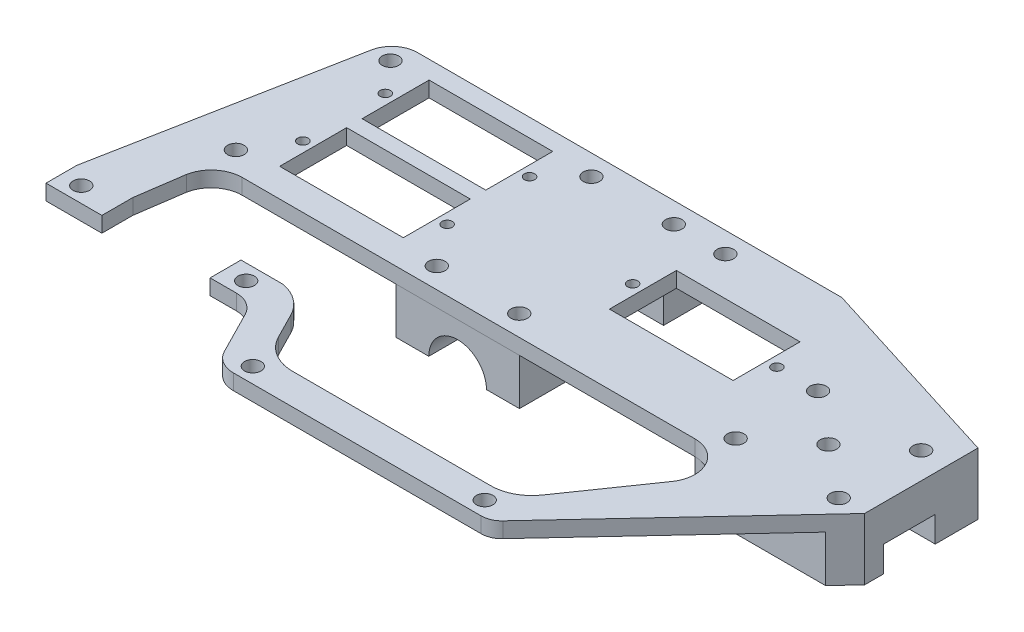
SolidWorks part; units mm, degrees
ref_plane "Спереди" through (0, 0, 0) normal (0, 0, 1) x (1, 0, 0)
ref_plane "Сверху" through (0, 0, 0) normal (0, 1, 0) x (1, 0, 0)
ref_plane "Справа" through (0, 0, 0) normal (1, 0, 0) x (0, 0, -1)
sketch "Эскиз1" plane through (0, 0, 0) normal (0, 1, 0) x (1, 0, 0)
  line L0 (0, 20) -> (0, -20) construction
  line L1 (16, 6.5) -> (40, 6.5)
  line L2 (-40, 14.5) -> (-16, 14.5)
  line L3 (-40, 14.5) -> (-40, 1.5)
  line L4 (-40, 1.5) -> (-16, 1.5)
  line L5 (-16, 14.5) -> (-16, 1.5)
  line L6 (-40, 14.5) -> (-16, 1.5) construction
  line L7 (-40, 1.5) -> (-16, 14.5) construction
  line L8 (-40, -1.5) -> (-16, -1.5)
  line L9 (-40, -1.5) -> (-40, -14.5)
  line L10 (-40, -14.5) -> (-16, -14.5)
  line L11 (-16, -1.5) -> (-16, -14.5)
  line L12 (-40, -1.5) -> (-16, -14.5) construction
  line L13 (-40, -14.5) -> (-16, -1.5) construction
  line L14 (-28, 8) -> (-28, -8) construction
  line L15 (0, 20) -> (-56.8521, 20) construction
  line L16 (0, 20) -> (59.9648, 20) construction
  line L17 (0, -20) -> (57.5525, -20) construction
  line L18 (0, -20) -> (-56.8521, -20) construction
  line L19 (16, 6.5) -> (16, -6.5)
  line L20 (16, -6.5) -> (40, -6.5)
  line L21 (40, 6.5) -> (40, -6.5)
  line L22 (16, 6.5) -> (40, -6.5) construction
  line L23 (16, -6.5) -> (40, 6.5) construction
  line L24 (28, 20) -> (28, -20) construction
  line L25 (-56.8521, 14) -> (93.1479, 14) construction
  line L26 (-56.8521, -16) -> (93.1479, -16) construction
  line L27 (-40, -37) -> (-56, -37) construction
  line L28 (-40, -37) -> (-24, -37) construction
  line L29 (-40, -14.5) -> (-40, -37) construction
  line L30 (-59.8465, -34) -> (-19.8465, -34) construction
  line L31 (-19.8465, -34) -> (-19.8465, -40) construction
  line L32 (-19.8465, -40) -> (-59.8465, -40) construction
  line L33 (-59.8465, -40) -> (-59.8465, -34) construction
  line L34 (-59.8465, -34) -> (-49.8878, 18)
  line L35 (36.6127, 18) -> (-49.8878, 18)
  line L36 (36.6127, 18) -> (75.1122, 5.9202)
  line L37 (-47.6771, -24.9007) -> (-49.0001, -34)
  line L38 (50, -16) -> (70, -16) construction
  line L39 (-59.8465, -34) -> (-59.8465, -40)
  line L40 (-59.8465, -40) -> (-19.8465, -40)
  line L41 (-19.8465, -40) -> (-14.2549, -50.9742)
  line L42 (-9.7998, -53.7042) -> (38.319, -53.7042)
  line L43 (75.1122, 5.9202) -> (75.1122, -16.0798)
  line L44 (50, 0) -> (50, -16) construction
  line L45 (-4.2859, -47.7018) -> (34.1658, -47.7018)
  line L46 (-49.0001, -34) -> (-22.2977, -34)
  line L47 (-13.9887, -38.2804) -> (-11.4139, -43.3337)
  line L48 (-41.7786, -20) -> (46.0945, -20)
  line L49 (40.7412, -44.2586) -> (51.0261, -29.4176)
  line L50 (-20.5914, -50.7042) -> (71.7063, -50.7042) construction
  line L51 (-20.5914, -53.7042) -> (73.7938, -53.7042) construction
  line L52 (0, -16) -> (0, -104.4432) construction
  line L53 (-47, 14) -> (-47, -16) construction
  line L54 (50, 0) -> (70, -16) construction
  line L55 (-44.6457, 8) -> (-11.6511, 8) construction
  line L56 (-47.6771, -8) -> (-3.6396, -8) construction
  line L57 (8, 0) -> (46.0945, 0) construction
  line L58 (50, 0) -> (70, 0) construction
  line L59 (75.1122, -16.0798) -> (41.2457, -52.4308)
  line L60 (-49.0001, -34) -> (-49.0001, -40) construction
  line L61 (-22.2977, -34) -> (-19.8465, -34)
  circle A0 centre (-8, 14) radius 1.6
  circle A1 centre (8, 14) radius 1.6
  circle A2 centre (-8, -16) radius 1.6
  circle A3 centre (8, -16) radius 1.6
  circle A4 centre (-47, 14) radius 1.6
  circle A5 centre (70, 0) radius 1.6
  circle A6 centre (50, 0) radius 1.6
  circle A7 centre (18, 14) radius 1.6
  circle A8 centre (-47, -16) radius 1.6
  circle A9 centre (-56, -37) radius 1.6
  circle A10 centre (-24, -37) radius 1.6
  circle A11 centre (50, -16) radius 1.6
  circle A12 centre (70, -16) radius 1.6
  arc A13 (-41.7786, -20) -> (-47.6771, -24.9007) centre (-41.7786, -26) ccw
  arc A14 (-19.8465, -34) -> (-13.9887, -38.2804) centre (-21.3286, -42.1767) cw
  arc A15 (-4.2859, -47.7018) -> (-11.4139, -43.3337) centre (-4.2859, -39.7018) cw
  arc A16 (40.7412, -44.2586) -> (34.1658, -47.7018) centre (34.1658, -39.7018) cw
  arc A17 (51.0261, -29.4176) -> (46.0945, -20) centre (46.0945, -26) ccw
  arc A18 (41.2457, -52.4308) -> (38.319, -53.7042) centre (38.319, -49.7042) cw
  arc A19 (-9.7998, -53.7042) -> (-14.2549, -50.9742) centre (-9.7998, -48.7042) cw
  circle A20 centre (-9, -50.7042) radius 1.6
  circle A21 centre (36, -50.7042) radius 1.6
  circle A22 centre (60, -8) radius 1.6
  circle A23 centre (-42, -8) radius 1
  circle A24 centre (-14, -8) radius 1
  circle A25 centre (-42, 8) radius 1
  circle A26 centre (-14, 8) radius 1
  circle A27 centre (14, 0) radius 1
  circle A28 centre (42, 0) radius 1
  point P2 (-28, 8)
  point P7 (0, 0)
  point P10 (28, 0)
  point P11 (-28, -8)
  point P35 (0, 14)
  point P41 (0, -16)
  point P77 (-46.7637, -20)
  point P86 (40.0593, -53.7042)
  point P92 (-49.0001, -34)
  dimension "D10" = 16
  dimension "D12" = 16
  dimension "D14" = 10
  dimension "D18" = 40
  dimension "D23" = 20
  dimension "D26" = 6
  dimension "D31" = 125
  dimension "D32" = 3
  dimension "D33" = 45
  dimension "D36" = 28
  dimension "D21" = 4
  dimension "D1" = 13
  dimension "D2" = 24
  dimension "D3" = 28
  dimension "D4" = 28
  dimension "D5" = 20
  dimension "D6" = 12
  dimension "D7" = 3
  dimension "D8" = 6
  dimension "D9" = 4
  dimension "D11" = 8
  dimension "D13" = 8
  dimension "D15" = 20
  dimension "D16" = 50
  dimension "D17" = 32
  dimension "D19" = 6
  dimension "D20" = 3
  dimension "D22" = 6.0024
  dimension "D24" = 14
  dimension "D25" = 36
  dimension "D27" = 6
  dimension "D29" = 14
  dimension "D30" = 22
  dimension "D34" = 40
  dimension "D35" = 47
  dimension "D37" = 28
  dimension "D38" = 28
  dimension "D39" = 14
  dimension "D40" = 14
  dimension "D41" = 14
  dimension "D42" = 16
  dimension "D43" = 2
extrude "Бобышка-Вытянуть1" add sketch "Эскиз1" along normal blind 3
sketch "Эскиз2" plane through (0, 0, 0) normal (0, 1, 0) x (1, 0, 0)
  line L0 (46.1017, 15.0227) -> (46.0945, -20)
  line L2 (75.1122, 5.9202) -> (36.6127, 18) construction
  line L4 (46.0945, -20) -> (71.46, -20)
  line L10 (0, 18) -> (0, -19.9611) construction
  line L11 (12, 8) -> (-12, 8)
  line L12 (12, 8) -> (12, 18)
  line L13 (12, 18) -> (-12, 18)
  line L14 (-12, 8) -> (-12, 18)
  line L15 (12, 8) -> (-12, 18) construction
  line L16 (12, 18) -> (-12, 8) construction
  line L17 (12, -19.9611) -> (-12, -19.9611)
  line L18 (12, -19.9611) -> (12, -9.9611)
  line L19 (12, -9.9611) -> (-12, -9.9611)
  line L20 (-12, -19.9611) -> (-12, -9.9611)
  line L21 (12, -19.9611) -> (-12, -9.9611) construction
  line L22 (12, -9.9611) -> (-12, -19.9611) construction
  line L24 (75.1122, -16.0798) -> (75.1122, 5.9202)
  line L25 (41.2457, -52.4308) -> (75.1122, -16.0798) construction
  line L26 (71.46, -20) -> (75.1122, -16.0798)
  line L27 (46.1017, 15.0227) -> (75.1122, 5.9202)
  line L28 (36.6127, 18) -> (-49.8878, 18) construction
  circle A0 centre (50, 0) radius 1.6
  circle A1 centre (70, 0) radius 1.6
  circle A2 centre (70, -16) radius 1.6
  circle A3 centre (50, -16) radius 1.6
  circle A4 centre (-8, 14) radius 1.6
  circle A5 centre (8, 14) radius 1.6
  circle A6 centre (-8, -16) radius 1.6
  circle A7 centre (8, -16) radius 1.6
  circle A12 centre (60, -8) radius 1.6
  point P26 (0, 13)
  point P35 (0, -14.9611)
  point P65 (0, 18)
  dimension "D2" = 24
extrude "Бобышка-Вытянуть2" add sketch "Эскиз2" against normal blind 9
sketch "Эскиз3" plane through (75.1122, 0, 0) normal (1, 0, 0) x (0, 0, -1)
  line L0 (-16.0798, -9) -> (5.9202, -9) construction
  line L1 (-12.3846, -14) -> (-2.3846, -14)
  line L2 (-12.3846, -14) -> (-12.3846, -4)
  line L3 (-12.3846, -4) -> (-2.3846, -4)
  line L4 (-2.3846, -14) -> (-2.3846, -4)
  line L6 (-12.3846, -4) -> (-2.3846, -14) construction
  line L8 (-2.3846, -4) -> (-12.3846, -14) construction
  line L9 (-18.1996, 12.1365) -> (3.7449, 12.1365) construction
  point P8 (-7.3846, -9)
  dimension "D1" = 10
extrude "Вырез-Вытянуть1" cut sketch "Эскиз3" against normal blind 20
sketch "Эскиз4" plane through (0, 0, -18) normal (0, 0, -1) x (-1, 0, 0)
  line L1 (-12, -9) -> (12, -9) construction
  circle A0 centre (0, -9) radius 4
extrude "Вырез-Вытянуть2" cut sketch "Эскиз4" against normal through all
sketch "Эскиз6" plane through (0, 0, -18) normal (0, 0, -1) x (-1, 0, 0)
  circle A0 centre (0, -9) radius 5.6
extrude "Вырез-Вытянуть3" cut sketch "Эскиз6" against normal blind 5
sketch "Эскиз7" plane through (0, 0, 19.9611) normal (0, 0, 1) x (1, 0, 0)
  circle A0 centre (0, -9) radius 5.6
extrude "Вырез-Вытянуть4" cut sketch "Эскиз7" against normal blind 6
fillet "Скругление5" radius 5 1 edges at (-49.8878, 1.5, -18)
fillet "Скругление6" radius 5 1 edges at (-19.8465, 1.5, 40)
sketch "Эскиз8" plane through (0, 3, 0) normal (0, 1, 0) x (1, 0, 0)
  line L0 (-49.0001, -34) -> (-49.0001, -40)
  line L1 (-59.8465, -40) -> (-22.9105, -40) construction
  line L2 (-49.0001, -40) -> (-28.0001, -40)
  line L3 (-28.0001, -40) -> (-28.0001, -34)
  line L4 (-49.0001, -34) -> (-19.8465, -34) construction
  line L5 (-28.0001, -34) -> (-49.0001, -34)
  dimension "D1" = 21
extrude "Вырез-Вытянуть5" cut sketch "Эскиз8" against normal through all
